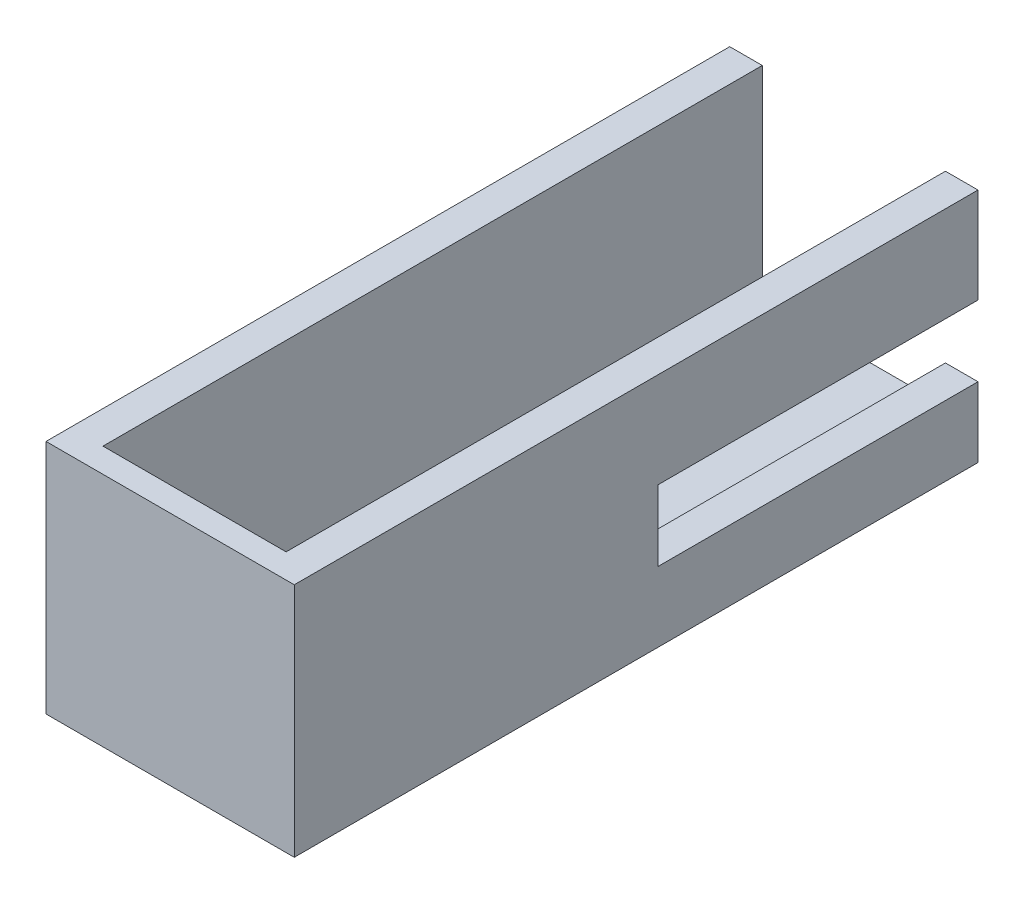
SolidWorks part; units mm, degrees
ref_plane "Front Plane" through (0, 0, 0) normal (0, 0, 1) x (1, 0, 0)
ref_plane "Top Plane" through (0, 0, 0) normal (0, 1, 0) x (1, 0, 0)
ref_plane "Right Plane" through (0, 0, 0) normal (1, 0, 0) x (0, 0, -1)
sketch "Sketch1" plane through (0, 0, 0) normal (0, 0, 1) x (1, 0, 0)
  line L0 (-9.8486, 0) -> (-9.8486, -25)
  line L1 (-9.8486, -25) -> (12.6514, -25)
  line L2 (12.6514, -25) -> (12.6514, 0)
  line L3 (12.6514, 0) -> (16.6514, 0)
  line L4 (16.6514, 0) -> (16.6514, -29)
  line L5 (16.6514, -29) -> (-13.8486, -29)
  line L6 (-13.8486, -29) -> (-13.8486, 0)
  line L7 (-13.8486, 0) -> (-9.8486, 0)
  dimension "D1" = 30.5
  dimension "D2" = 4
  dimension "D3" = 4
  dimension "D4" = 25
extrude "Boss-Extrude1" add sketch "Sketch1" along normal mid plane 84
sketch "Sketch2" plane through (0, 0, 42) normal (0, 0, 1) x (1, 0, 0)
  line L1 (-13.8486, 0) -> (16.6514, 0)
  line L2 (-13.8486, 0) -> (-13.8486, -29)
  line L3 (-13.8486, -29) -> (16.6514, -29)
  line L4 (16.6514, 0) -> (16.6514, -29)
extrude "Boss-Extrude2" add sketch "Sketch2" against normal blind 3
sketch "Sketch3" plane through (0, 0, 0) normal (1, 0, 0) x (0, 0, -1)
  line L1 (2.6591, -20.398) -> (42.6591, -20.398)
  line L2 (2.6591, -20.398) -> (2.6591, -11.708)
  line L3 (2.6591, -11.708) -> (42.6591, -11.708)
  line L4 (42.6591, -20.398) -> (42.6591, -11.708)
  line L5 (2.6591, -20.398) -> (42.6591, -11.708) construction
  line L6 (2.6591, -11.708) -> (42.6591, -20.398) construction
  point P0 (22.6591, -16.053)
  dimension "D1" = 40
  dimension "D2" = 8.69
extrude "Cut-Extrude1" cut sketch "Sketch3" along normal blind 30
